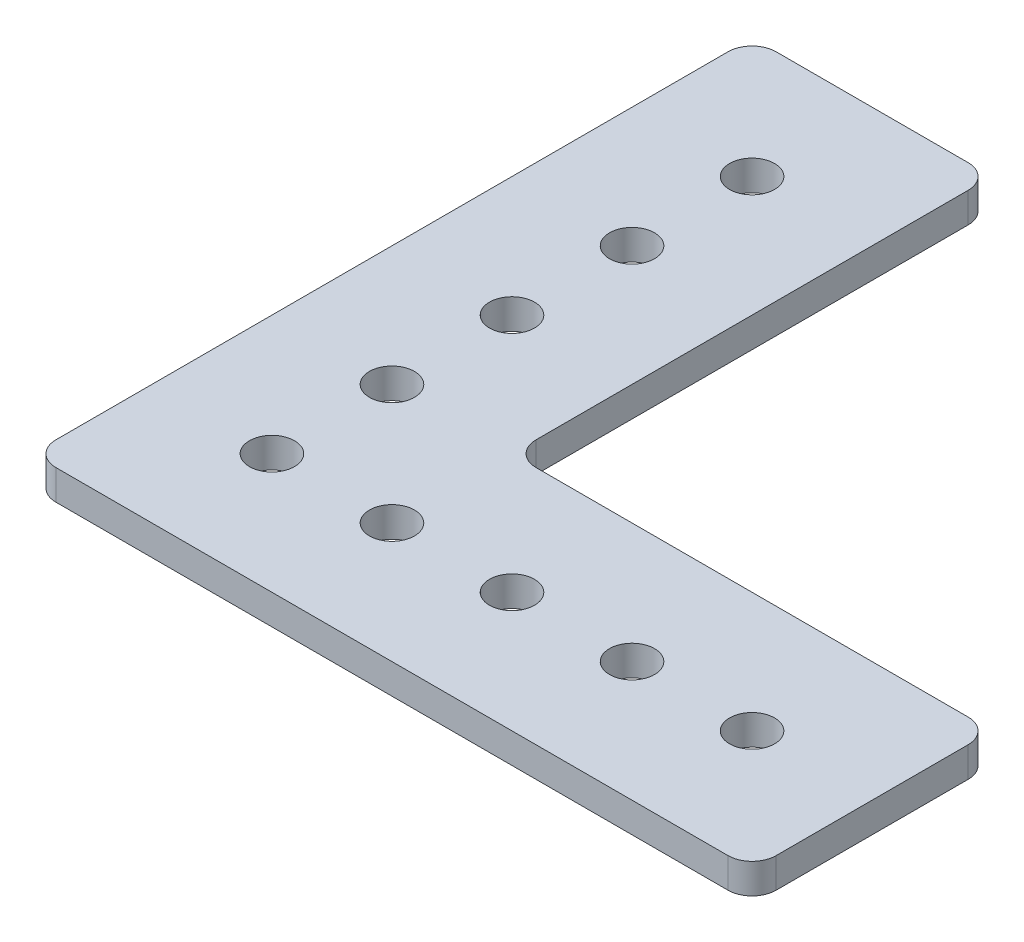
SolidWorks part; units mm, degrees
material "1060 Alloy"
ref_plane "Front Plane" through (0, 0, 0) normal (0, 0, 1) x (1, 0, 0)
ref_plane "Top Plane" through (0, 0, 0) normal (0, 1, 0) x (1, 0, 0)
ref_plane "Right Plane" through (0, 0, 0) normal (1, 0, 0) x (0, 0, -1)
sketch "Sketch1" plane through (0, 0, 0) normal (0, 1, 0) x (1, 0, 0)
  line L1 (2.54, 0) -> (25.4, 0)
  line L2 (0, 2.54) -> (0, 73.66)
  line L3 (2.54, 76.2) -> (22.86, 76.2)
  line L4 (25.4, 27.94) -> (25.4, 73.66)
  line L5 (0, 0) -> (73.66, 0)
  line L6 (0, 0) -> (0, 25.4)
  line L7 (27.94, 25.4) -> (73.66, 25.4)
  line L8 (76.2, 2.54) -> (76.2, 22.86)
  circle A0 centre (12.7, 12.7) radius 2.3813
  circle A1 centre (25.4, 12.7) radius 2.3813
  circle A2 centre (38.1, 12.7) radius 2.3812
  circle A3 centre (50.8, 12.7) radius 2.3812
  circle A4 centre (12.7, 25.4) radius 2.3813
  circle A5 centre (12.7, 38.1) radius 2.3812
  circle A6 centre (12.7, 50.8) radius 2.3812
  arc A7 (0, 2.54) -> (2.54, 0) centre (2.54, 2.54) ccw
  arc A8 (73.66, 0) -> (76.2, 2.54) centre (73.66, 2.54) ccw
  arc A9 (76.2, 22.86) -> (73.66, 25.4) centre (73.66, 22.86) ccw
  arc A10 (27.94, 25.4) -> (25.4, 27.94) centre (27.94, 27.94) cw
  arc A11 (25.4, 73.66) -> (22.86, 76.2) centre (22.86, 73.66) ccw
  arc A12 (0, 73.66) -> (2.54, 76.2) centre (2.54, 73.66) cw
  circle A13 centre (12.7, 63.5) radius 2.3812
  circle A14 centre (63.5, 12.7) radius 2.3813
  point P28 (76.2, 0)
  point P31 (76.2, 25.4)
  point P36 (25.4, 76.2)
  point P39 (0, 76.2)
  dimension "D5" = 4.7625
  dimension "D6" = 4.7625
  dimension "3/16" = 4.7625
  dimension "D8" = 4.7625
  dimension "D9" = 12.7
  dimension "D10" = 12.7
  dimension "D11" = 12.7
  dimension "D12" = 12.7
  dimension "D13" = 12.7
  dimension "D14" = 12.7
  dimension "D15" = 12.7
  dimension "D16" = 12.7
  dimension "D17" = 4.7625
  dimension "D18" = 12.7
  dimension "D19" = 4.7625
  dimension "D20" = 12.7
  dimension "D21" = 4.7625
  dimension "D22" = 12.7
  dimension "D23" = 12.7
  dimension "D24" = 12.7
  dimension "D25" = 12.7
  dimension "D26" = 2.54
  dimension "D27" = 4.7625
  dimension "D29" = 4.7625
  dimension "D1" = 76.2
  dimension "D2" = 76.2
  dimension "D3" = 25.4
  dimension "D4" = 25.4
  dimension "D28" = 12.7
  dimension "D30" = 12.7
extrude "Boss-Extrude1" add sketch "Sketch1" along normal blind 3.175 contours A12 L2 A7 L1 L5 A8 L8 A9 L7 A10 L4 A11 L3 A6 A5 A4 A3 A2 A1 A0
